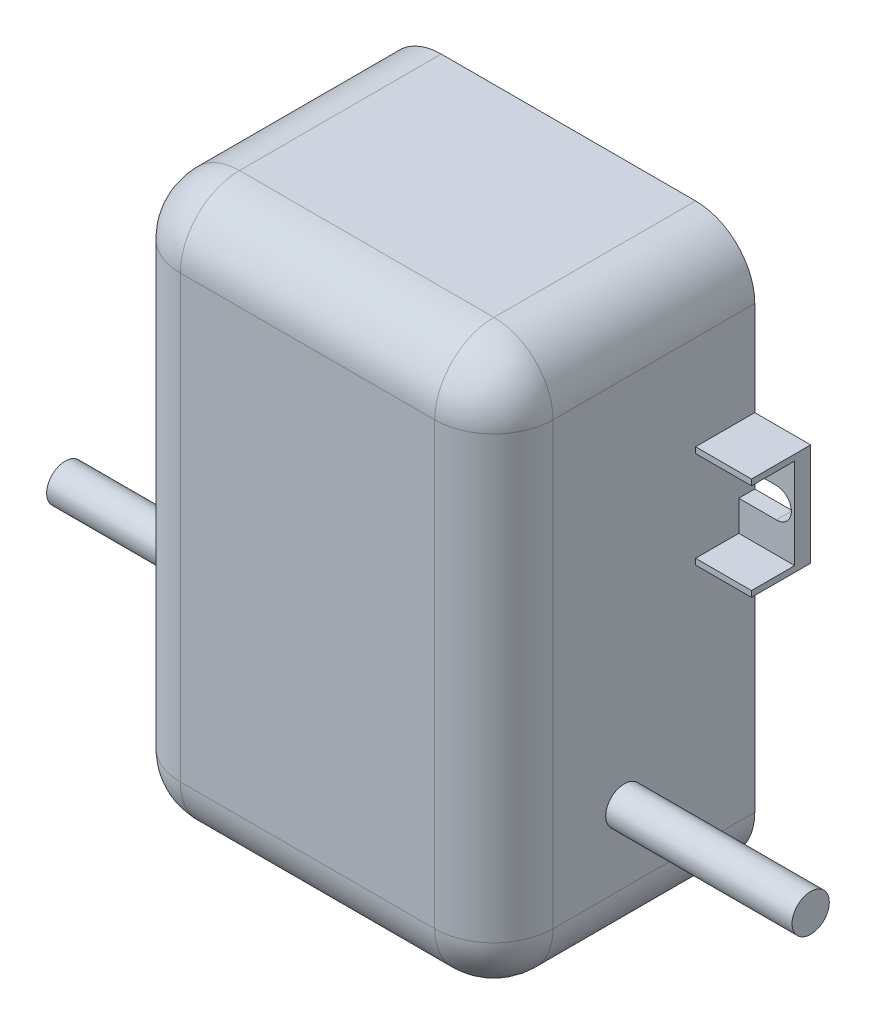
SolidWorks part; units mm, degrees
ref_plane "Front Plane" through (0, 0, 0) normal (0, 0, 1) x (1, 0, 0)
ref_plane "Top Plane" through (0, 0, 0) normal (0, 1, 0) x (1, 0, 0)
ref_plane "Right Plane" through (0, 0, 0) normal (1, 0, 0) x (0, 0, -1)
sketch "Sketch1" plane through (0, 0, 0) normal (0, 0, 1) x (1, 0, 0)
  line L1 (-20, -30) -> (20, -30)
  line L2 (-20, -30) -> (-20, 30)
  line L3 (-20, 30) -> (20, 30)
  line L4 (20, -30) -> (20, 30)
  line L5 (-20, -30) -> (20, 30) construction
  line L6 (-20, 30) -> (20, -30) construction
  point P0 (0, 0)
  dimension "D1" = 40
  dimension "D2" = 60
extrude "Boss-Extrude1" add sketch "Sketch1" along normal blind 28
sketch "Sketch2" plane through (0, 0, 0) normal (0, 0, -1) x (-1, 0, 0)
  line L0 (-20, -30) -> (-20, 30) construction
  line L1 (-20, 13.5) -> (-26, 13.5)
  line L2 (-20, 13.5) -> (-20, 2.5)
  line L3 (-20, 2.5) -> (-26, 2.5)
  line L4 (-26, 13.5) -> (-26, 2.5)
  line L5 (-28.5907, 8) -> (-12.6211, 8) construction
  line L7 (20, -30) -> (-20, -30) construction
  line L8 (-20, 8) -> (-24.0383, 8) construction
  line L9 (-20, 6.4) -> (-24.0383, 6.4)
  line L10 (-20, 9.6) -> (-24.0383, 9.6)
  line L11 (0, 30) -> (0, -29.7069) construction
  line L12 (-20, 30) -> (20, 30) construction
  line L13 (20, 8) -> (24.0383, 8) construction
  line L14 (20, 6.4) -> (24.0383, 6.4)
  line L15 (20, 9.6) -> (24.0383, 9.6)
  line L16 (20, 2.5) -> (26, 2.5)
  line L17 (26, 13.5) -> (26, 2.5)
  line L18 (20, 13.5) -> (26, 13.5)
  arc A0 (-20, 6.4) -> (-20, 9.6) centre (-20, 8) ccw
  arc A1 (-24.0383, 9.6) -> (-24.0383, 6.4) centre (-24.0383, 8) ccw
  arc A2 (20, 6.4) -> (20, 9.6) centre (20, 8) cw
  arc A3 (24.0383, 9.6) -> (24.0383, 6.4) centre (24.0383, 8) cw
  point P12 (-22.0192, 8)
  point P24 (22.0192, 8)
  line M1 (-20, 30) -> (-20, -30)
  line M3 (20, -30) -> (20, 30)
  dimension "D1" = 6
  dimension "D2" = 38
  dimension "D3" = 5.5
  dimension "D4" = 11
  dimension "D5" = 3.2
extrude "Boss-Extrude2" add sketch "Sketch2" against normal blind 6.35 contours A1 L10 L1 L4 L3 L2 L9 M1 | L15 A3 L14 L16 L17 L18 M3
fillet "Fillet1" radius 6.35 8 edges at (-20, -30, 14) (20, -30, 14) (0, -30, 28) (20, 0, 28) (20, 30, 14) (-20, 0, 28) (0, 30, 28) (-20, 30, 14)
sketch "Sketch4" plane through (0, 0, 6.35) normal (0, 0, 1) x (1, 0, 0)
  line L0 (-20, 2.5) -> (-20, 6.4) construction
  line L1 (-28.7903, 12.865) -> (-20, 12.865)
  line L2 (-28.7903, 12.865) -> (-28.7903, 3.135)
  line L3 (-28.7903, 3.135) -> (-20, 3.135)
  line L4 (-20, 12.865) -> (-20, 3.135)
  line L5 (-20, 2.5) -> (-26, 2.5) construction
  line L6 (-20, 13.5) -> (-26, 13.5) construction
  line L7 (0, 23.65) -> (0, -23.65) construction
  line L8 (13.65, 23.65) -> (-13.65, 23.65) construction
  line L9 (-13.65, -23.65) -> (13.65, -23.65) construction
  line L10 (20, 12.865) -> (20, 3.135)
  line L11 (28.7903, 3.135) -> (20, 3.135)
  line L12 (28.7903, 12.865) -> (28.7903, 3.135)
  line L13 (28.7903, 12.865) -> (20, 12.865)
  dimension "D1" = 0.635
  dimension "D2" = 0.635
extrude "Cut-Extrude1" cut sketch "Sketch4" against normal blind 4.6355
sketch "Sketch5" plane through (0, 0, 0) normal (1, 0, 0) x (0, 0, -1)
  line L0 (0, 2.5) -> (0, -23.65) construction
  line L1 (-21.65, -30) -> (0, -30) construction
  circle A0 centre (-14, -16) radius 2
  dimension "D3" = 4
  dimension "D1" = 14
  dimension "D2" = 14
extrude "Boss-Extrude3" add sketch "Sketch5" along normal mid plane 80
